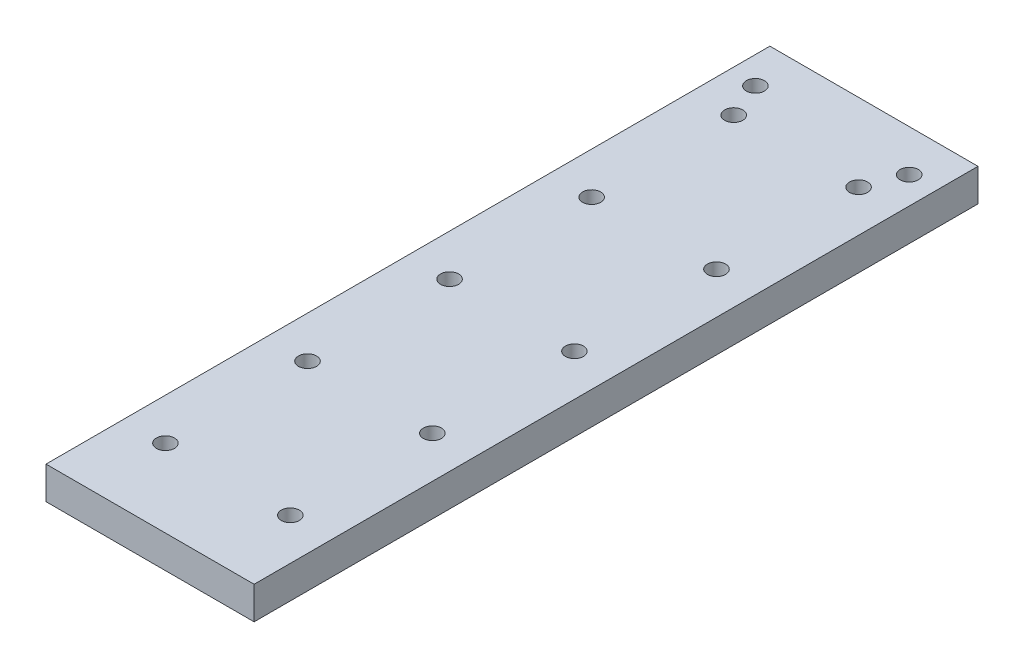
SolidWorks part; units mm, degrees
ref_plane "Front Plane" through (0, 0, 0) normal (0, 0, 1) x (1, 0, 0)
ref_plane "Top Plane" through (0, 0, 0) normal (0, 1, 0) x (1, 0, 0)
ref_plane "Right Plane" through (0, 0, 0) normal (1, 0, 0) x (0, 0, -1)
sketch "Sketch1" plane through (0, 0, 0) normal (0, 1, 0) x (1, 0, 0)
  line L1 (-57.5, -200) -> (57.5, -200)
  line L2 (-57.5, -200) -> (-57.5, 200)
  line L3 (-57.5, 200) -> (57.5, 200)
  line L4 (57.5, -200) -> (57.5, 200)
  line L5 (-57.5, -200) -> (57.5, 200) construction
  line L6 (-57.5, 200) -> (57.5, -200) construction
  point P0 (0, 0)
  dimension "D1" = 115
  dimension "D2" = 400
extrude "Boss-Extrude1" add sketch "Sketch1" along normal blind 18
sketch "Sketch2" plane through (0, 18, 0) normal (0, 1, 0) x (1, 0, 0)
  line L0 (-57.5, 177) -> (57.5, 177) construction
  line L1 (-57.5, 200) -> (-57.5, -200) construction
  line L2 (57.5, -200) -> (57.5, 200) construction
  line L3 (57.5, 200) -> (-57.5, 200) construction
  line L4 (0, 200) -> (0, 177) construction
  line L5 (34.5, 200) -> (34.5, -200) construction
  line L6 (-57.5, -200) -> (57.5, -200) construction
  line L7 (34.5, 157) -> (-57.5, 157) construction
  line L8 (0, 0) -> (0, 157) construction
  line L9 (0, 0) -> (96.5887, 0) construction
  line L10 (-34.5, 78.5) -> (34.5, 78.5) construction
  circle A0 centre (-42.5, 177) radius 5
  circle A1 centre (42.5, 177) radius 5
  circle A2 centre (34.5, 157) radius 5
  circle A3 centre (34.5, 78.5) radius 5
  circle A4 centre (34.5, 0) radius 5
  circle A5 centre (34.5, -78.5) radius 5
  circle A6 centre (34.5, -157) radius 5
  circle A7 centre (-34.5, -157) radius 5
  circle A8 centre (-34.5, -78.5) radius 5
  circle A9 centre (-34.5, 0) radius 5
  circle A10 centre (-34.5, 78.5) radius 5
  circle A11 centre (-34.5, 157) radius 5
  point P34 (0, 78.5)
  dimension "D2" = 15
  dimension "D3" = 23
  dimension "D4" = 20
  dimension "D1" = 23
extrude "Cut-Extrude1" cut sketch "Sketch2" against normal through all
